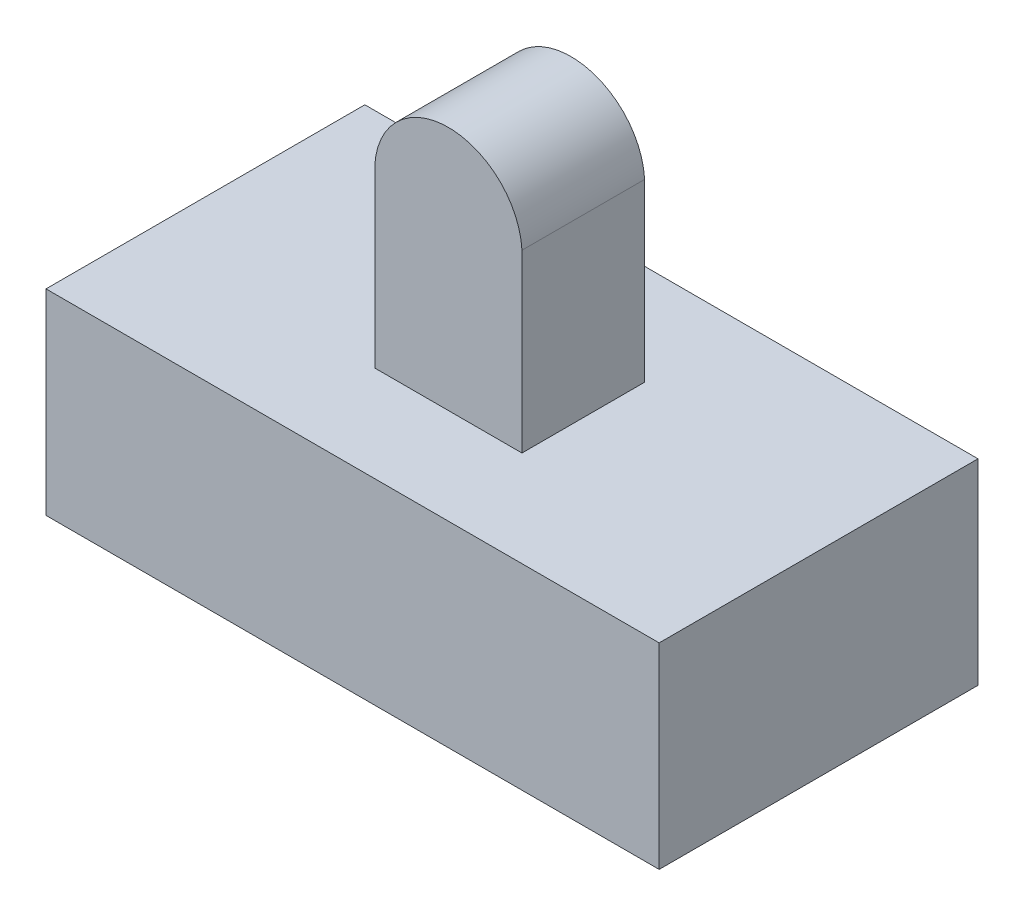
SolidWorks part; units mm, degrees
ref_plane "Front Plane" through (0, 0, 0) normal (0, 0, 1) x (1, 0, 0)
ref_plane "Top Plane" through (0, 0, 0) normal (0, 1, 0) x (1, 0, 0)
ref_plane "Right Plane" through (0, 0, 0) normal (1, 0, 0) x (0, 0, -1)
sketch "Sketch3" plane through (0, 0, 0) normal (0, 1, 0) x (1, 0, 0)
  line L1 (-5.8247, 4.6907) -> (19.1753, 4.6907)
  line L2 (-5.8247, 4.6907) -> (-5.8247, -8.3093)
  line L3 (-5.8247, -8.3093) -> (19.1753, -8.3093)
  line L4 (19.1753, 4.6907) -> (19.1753, -8.3093)
  dimension "D1" = 13
  dimension "D2" = 25
extrude "Boss-Extrude1" add sketch "Sketch3" along normal blind 8
sketch "Sketch4" plane through (0, 0, 0) normal (0, -1, 0) x (1, 0, 0)
  line L1 (9.5687, 4.202) -> (3.5687, 4.202)
  line L2 (9.5687, 4.202) -> (9.5687, 0.002)
  line L3 (9.5687, 0.002) -> (3.5687, 0.002)
  line L4 (3.5687, 4.202) -> (3.5687, 0.002)
  dimension "D1" = 4.2
  dimension "D2" = 6
extrude "Cut-Extrude1" cut sketch "Sketch4" against normal blind 7
sketch "Sketch5" plane through (0, 8, 0) normal (0, 1, 0) x (1, 0, 0)
  line L0 (9.6753, 0.5975) -> (3.6753, 0.5975)
  line L1 (9.6753, 0.5975) -> (9.6753, -4.4025)
  line L2 (9.6753, -4.4025) -> (3.6753, -4.4025)
  line L3 (3.6753, 0.5975) -> (3.6753, -4.4025)
  line L4 (19.1753, -8.3093) -> (19.1753, 4.6907) construction
  line L5 (-5.8247, 4.6907) -> (-5.8247, -8.3093) construction
  dimension "D1" = 9.5
  dimension "D2" = 9.5
  dimension "D3" = 5
extrude "Boss-Extrude2" add sketch "Sketch5" along normal blind 10
sketch "Sketch6" plane through (0, 0, -0.5975) normal (0, 0, -1) x (-1, 0, 0)
  line L0 (-9.6753, 18) -> (-9.6753, 8) construction
  line L1 (-3.6753, 18) -> (-3.6753, 8) construction
  line L2 (-9.6753, 14.8295) -> (-9.6753, 18)
  line L3 (-9.6753, 18) -> (-3.6753, 18)
  line L4 (-3.6753, 18) -> (-3.6753, 14.8295)
  arc A0 (-9.6753, 14.8295) -> (-3.6753, 14.8295) centre (-6.6753, 14.9954) cw
  line M3 (-3.6753, 18) -> (-9.6753, 18)
  line M4 (-9.6753, 18) -> (-9.6753, 8)
extrude "Cut-Extrude2" cut sketch "Sketch6" against normal blind 10 contours A0 L4 M3 | A0 L3 M4
